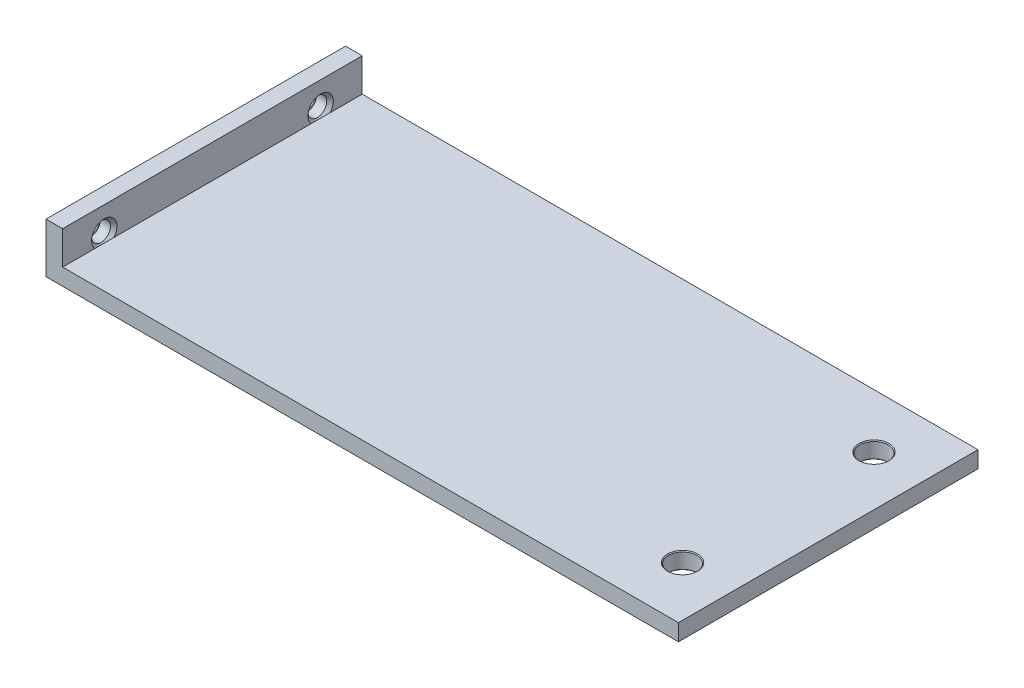
SolidWorks part; units mm, degrees
ref_plane "Спереди" through (0, 0, 0) normal (0, 0, 1) x (1, 0, 0)
ref_plane "Сверху" through (0, 0, 0) normal (0, 1, 0) x (1, 0, 0)
ref_plane "Справа" through (0, 0, 0) normal (1, 0, 0) x (0, 0, -1)
sketch "Эскиз1" plane through (0, 0, 0) normal (0, 0, 1) x (1, 0, 0)
  line L0 (-38, 18) -> (38, 18)
  line L1 (-40, -20) -> (40, -20)
  line L2 (-40, -20) -> (-40, 20)
  line L3 (-40, 20) -> (40, 20)
  line L4 (40, -20) -> (40, 20)
  line L5 (-40, -20) -> (40, 20) construction
  line L6 (-40, 20) -> (40, -20) construction
  line L7 (38, -18) -> (38, 18)
  line L8 (-38, -18) -> (38, -18)
  line L9 (-38, -18) -> (-38, 18)
  point P0 (0, 0)
  dimension "D1" = 80
  dimension "D2" = 40
  dimension "D3" = 2
extrude "Бобышка-Вытянуть1" add sketch "Эскиз1" along normal blind 36
sketch "Эскиз2" plane through (0, 0, 36) normal (0, 0, 1) x (1, 0, 0)
  line L0 (-40, -14) -> (36, -14)
  line L1 (-40, 20) -> (-40, -20) construction
  line L2 (36, -14) -> (36, -20)
  line L3 (-40, -20) -> (40, -20) construction
  line M1 (40, -20) -> (40, 20)
  line M2 (40, 20) -> (-40, 20)
  line M3 (-40, 20) -> (-40, -20)
  line M4 (-40, -20) -> (40, -20)
  line M5 (-38, -18) -> (-38, 18)
  line M6 (-38, 18) -> (38, 18)
  line M7 (38, 18) -> (38, -18)
  line M8 (38, -18) -> (-38, -18)
  dimension "D1" = 6
  dimension "D2" = 76
extrude "Вырез-Вытянуть1" cut sketch "Эскиз2" against normal through all contours L2 L0 M8 M4 M1 M2 M3 M5 M6 M7
hole_wizard "4-40" positions "Эскиз4" profile "Эскиз3" tap size "#4-40" standard "Ansi (в дюймах)" end condition up to next
sketch "Эскиз4" plane through (-40, 0, 0) normal (-1, 0, 0) x (0, 0, 1)
  line L0 (36, -20) -> (0, -20) construction
  line L1 (0, -14) -> (0, -20) construction
  point P0 (5, -17)
  point P1 (31, -17)
  dimension "D1" = 3
  dimension "D2" = 5
  dimension "D3" = 26
cosmetic thread "Отверстие резьбы1" parameters "D2"=2.8448
cosmetic thread "Отверстие резьбы2" parameters "D2"=2.8448
sketch "Эскиз3" plane through (-40, -17, 5) normal (0, 1, 0) x (0, 0, 1)
  line L0 (0, 0) -> (0, 2)
  line L1 (0, 2) -> (1.524, 2)
  line L2 (1.1303, 1.6063) -> (1.1303, 0.3937)
  line L3 (1.1303, 0.3937) -> (1.524, 0)
  line L5 (1.524, 0) -> (0, 0)
  line L6 (-1.1303, 0.3937) -> (-1.524, 0) construction
  line L7 (1.524, 2) -> (1.1303, 1.6063)
  line L8 (-1.524, 2) -> (-1.1303, 1.6063) construction
  line L11 (0, -6.35) -> (0, 107.95) construction
  dimension "Диаметр проходного сверла" = 2.2606
  dimension "Глубина проходного сверла" = 2
  dimension "Диаметр передней зенковки" = 3.048
  dimension "Угол передней зенковки" = 90
  dimension "Диаметр задней зенковки" = 3.048
  dimension "Угол задней зенковки" = 90
hole_wizard "Отверстие под  M3" positions "Эскиз6" profile "Эскиз5" hole size "M3" standard "DIN" end condition up to next
sketch "Эскиз6" plane through (0, -18, 0) normal (0, 1, 0) x (-1, 0, 0)
  line L0 (40, 36) -> (40, 0) construction
  line L1 (38, 0) -> (-36, 0) construction
  point P0 (-30, 6.5)
  point P1 (-30, 29.5)
  dimension "D1" = 70
  dimension "D2" = 6.5
  dimension "D3" = 23
sketch "Эскиз5" plane through (30, -18, 6.5) normal (1, 0, 0) x (0, 0, 1)
  line L0 (0, 0) -> (0, 2)
  line L1 (0, 2) -> (1.8, 2)
  line L2 (1.7, 1.9) -> (1.7, 0.1)
  line L3 (1.7, 0.1) -> (1.8, 0)
  line L5 (1.8, 0) -> (0, 0)
  line L6 (-1.7, 0.1) -> (-1.8, 0) construction
  line L7 (1.8, 2) -> (1.7, 1.9)
  line L8 (-1.8, 2) -> (-1.7, 1.9) construction
  line L11 (0, -6.35) -> (0, 107.95) construction
  dimension "Диаметр сквозного отверстия" = 3.4
  dimension "Глубина сквозного отверстия" = 2
  dimension "Диаметр передней зенковки" = 3.6
  dimension "Угол передней зенковки" = 90
  dimension "Диаметр задней зенковки" = 3.6
  dimension "Угол задней зенковки" = 90
